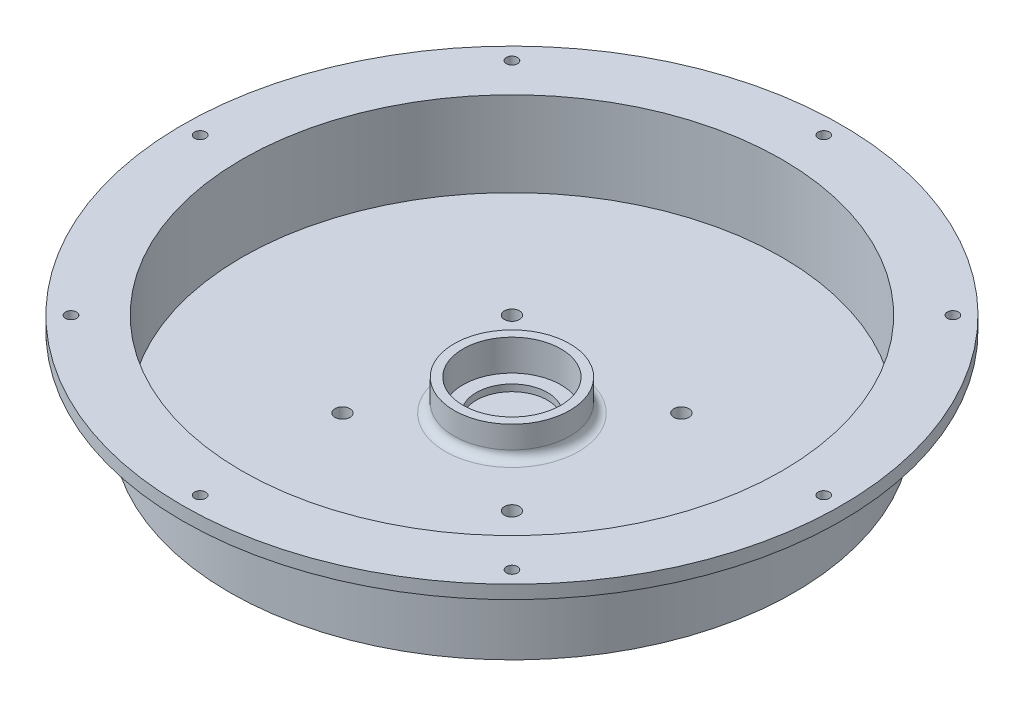
SolidWorks part; units mm, degrees
material "6061 Alloy"
ref_plane "Front Plane" through (0, 0, 0) normal (0, 0, 1) x (1, 0, 0)
ref_plane "Top Plane" through (0, 0, 0) normal (0, 1, 0) x (1, 0, 0)
ref_plane "Right Plane" through (0, 0, 0) normal (1, 0, 0) x (0, 0, -1)
sketch "Sketch1" plane through (0, 0, 0) normal (0, 1, 0) x (1, 0, 0)
  circle A0 centre (0, 0) radius 59.69 construction
  circle A1 centre (0, 0) radius 60.69
  circle A2 centre (0, 0) radius 63.5
  dimension "D1" = 127
  dimension "D2" = 121.38
  dimension "D3" = 119.38
  dimension "D4" = 0
extrude "Boss-Extrude1" add sketch "Sketch1" along normal blind 22.225 contours A2 | A1
sketch "Sketch3" plane through (0, 0, 0) normal (0, 1, 0) x (1, 0, 0)
  circle A0 centre (0, 0) radius 63.5
extrude "Boss-Extrude2" add sketch "Sketch3" along normal blind 3.175
sketch "Sketch8" plane through (0, 3.175, 0) normal (0, 1, 0) x (1, 0, 0)
  circle A0 centre (0, 0) radius 11
  circle A1 centre (0, 0) radius 13
  dimension "D1" = 22
  dimension "D2" = 26
extrude "Boss-Extrude4" add sketch "Sketch8" along normal blind 7
sketch "Sketch10" plane through (0, 22.225, 0) normal (0, 1, 0) x (1, 0, 0)
  circle A0 centre (0, 0) radius 63.5
  circle A1 centre (0, 0) radius 74.095
  dimension "D1" = 127
  dimension "D2" = 148.19
extrude "Boss-Extrude5" add sketch "Sketch10" against normal blind 3
sketch "Sketch15" plane through (0, 22.225, 0) normal (0, 1, 0) x (1, 0, 0)
  point P0 (-70.1, 0)
  dimension "D1" = 70.1
hole_wizard "M3x0.5 Tapped Hole1" positions "Sketch15" profile "Sketch14" tap size "M3x0.5" standard "ANSI Metric" end condition through all
sketch "Sketch14" plane through (-70.1, 22.225, 0) normal (1, 0, 0) x (0, 0, 1)
  line L0 (0, 0) -> (0, 22.225)
  line L1 (0, 22.225) -> (1.25, 22.225)
  line L2 (1.25, 22.225) -> (1.25, 0)
  line L5 (1.25, 0) -> (0, 0)
  line L11 (0, -6.35) -> (0, 107.95) construction
  dimension "Thru Tap Drill Dia." = 2.5
  dimension "Thru Tap Drill Depth" = 22.225
cosmetic thread "Hole Thread1" parameters "D2"=3
pattern_circular "CirPattern2" count 8 over 360 about axis through (0, 0, 0) along (0, 1, 0) of "M3x0.5 Tapped Hole1"
cosmetic thread "Hole Thread2" parameters "D2"=3
cosmetic thread "Hole Thread3" parameters "D2"=3
cosmetic thread "Hole Thread4" parameters "D2"=3
cosmetic thread "Hole Thread5" parameters "D2"=3
cosmetic thread "Hole Thread6" parameters "D2"=3
cosmetic thread "Hole Thread7" parameters "D2"=3
cosmetic thread "Hole Thread8" parameters "D2"=3
sketch "Sketch16" plane through (0, 3.175, 0) normal (0, 1, 0) x (1, 0, 0)
  circle A0 centre (0, 0) radius 8
  dimension "D1" = 16
extrude "Cut-Extrude1" cut sketch "Sketch16" against normal blind 1.5
fillet "Fillet1" radius 2 1 edges at (0, 3.175, 13)
fillet "Fillet2" radius 3 1 edges at (0, 19.225, 63.5)
sketch "Sketch18" plane through (0, 3.175, 0) normal (0, 1, 0) x (1, 0, 0)
  line L1 (-19.05, 19.05) -> (19.05, 19.05) construction
  line L2 (-19.05, 19.05) -> (-19.05, -19.05) construction
  line L3 (-19.05, -19.05) -> (19.05, -19.05) construction
  line L4 (19.05, 19.05) -> (19.05, -19.05) construction
  line L5 (-19.05, 19.05) -> (19.05, -19.05) construction
  line L6 (-19.05, -19.05) -> (19.05, 19.05) construction
  point P0 (0, 0)
  dimension "D1" = 38.1
  dimension "D2" = 38.1
sketch "Sketch19" plane through (0, 3.175, 0) normal (0, 1, 0) x (1, 0, 0)
  circle A0 centre (19.05, -19.05) radius 1.7
  circle A1 centre (19.05, 19.05) radius 1.7
  circle A2 centre (-19.05, -19.05) radius 1.7
  circle A3 centre (-19.05, 19.05) radius 1.7
  dimension "D1" = 3.4
  dimension "D2" = 3.4
  dimension "D3" = 3.4
  dimension "D4" = 3.4
extrude "Cut-Extrude2" cut sketch "Sketch19" against normal through all
